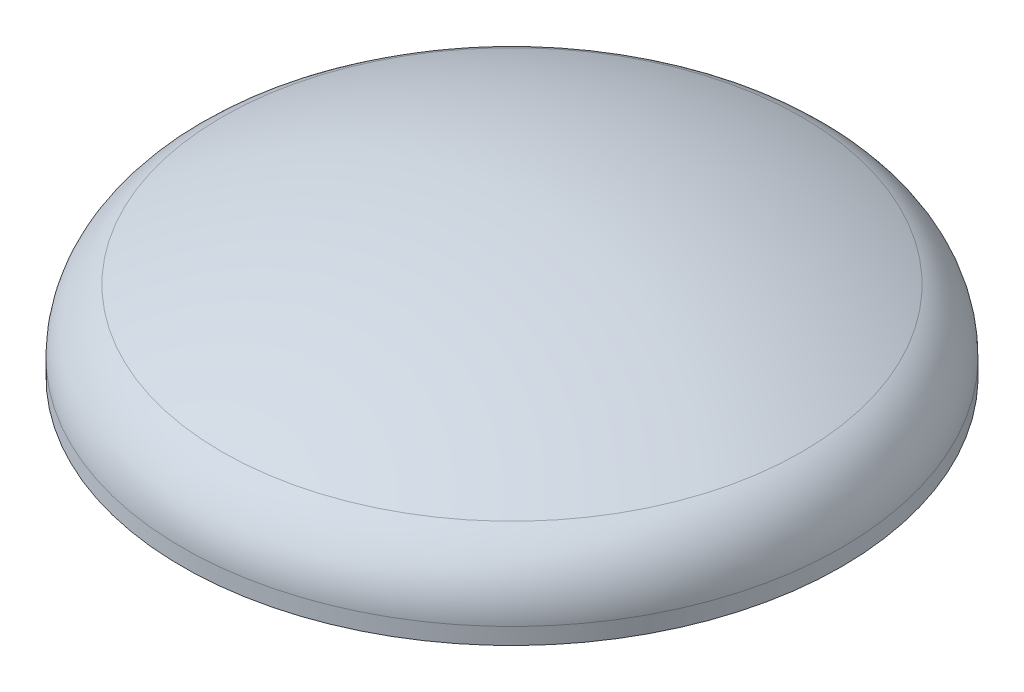
SolidWorks part; units mm, degrees
material "P265GH"
ref_plane "Ebene vorne" through (0, 0, 0) normal (0, 0, 1) x (1, 0, 0)
ref_plane "Ebene oben" through (0, 0, 0) normal (0, 1, 0) x (1, 0, 0)
ref_plane "Ebene rechts" through (0, 0, 0) normal (1, 0, 0) x (0, 0, -1)
other "Massenmittelpunkt"
other "Klopperböden"
sketch "Rotationsschnitt" plane through (0, 0, 0) normal (0, 0, 1) x (1, 0, 0)
  line L0 (-900, 0) -> (900, 0) construction
  line L2 (0, 0) -> (0, 387.84) construction
  line L6 (-900, 0) -> (-900, 45)
  line L7 (900, 0) -> (900, 45) construction
  line L8 (-888, 0) -> (-888, 45)
  line L9 (-900, 0) -> (-888, 0)
  line L10 (0, 399.84) -> (0, 387.84)
  line L11 (0, 387.84) -> (0, 399.84) construction
  arc A0 (900, 45) -> (791.973, 217.6016) centre (708.0983, 45) ccw construction
  arc A1 (-900, 45) -> (-791.973, 217.6016) centre (-708.0983, 45) cw
  arc A2 (-791.973, 217.6016) -> (0, 399.84) centre (0, -1412.16) cw
  arc A3 (2.3423, 399.8385) -> (791.973, 217.6016) centre (0, -1412.16) cw construction
  arc A4 (-888, 45) -> (-786.7281, 206.8084) centre (-708.0983, 45) cw
  arc A5 (-786.7281, 206.8084) -> (0, 387.84) centre (0, -1412.16) cw
  arc A6 (-786.7281, 206.8084) -> (0, 387.84) centre (0, -1412.16) cw construction
revolve "Klöpperboden" add sketch "Rotationsschnitt" angle 360 about L2
ref_plane "Ebene 45°" through (0, 0, 0) normal (-0.7071, 0, 0.7071) x (0.7071, 0, 0.7071)
equation "\"R innen@Rotationsschnitt\"=\"D außen@Rotationsschnitt\""
equation "\"H2@Rotationsschnitt\"=(0.1935*\"D außen@Rotationsschnitt\")-(0.455*\"s Dicke@Rotationsschnitt\")"
